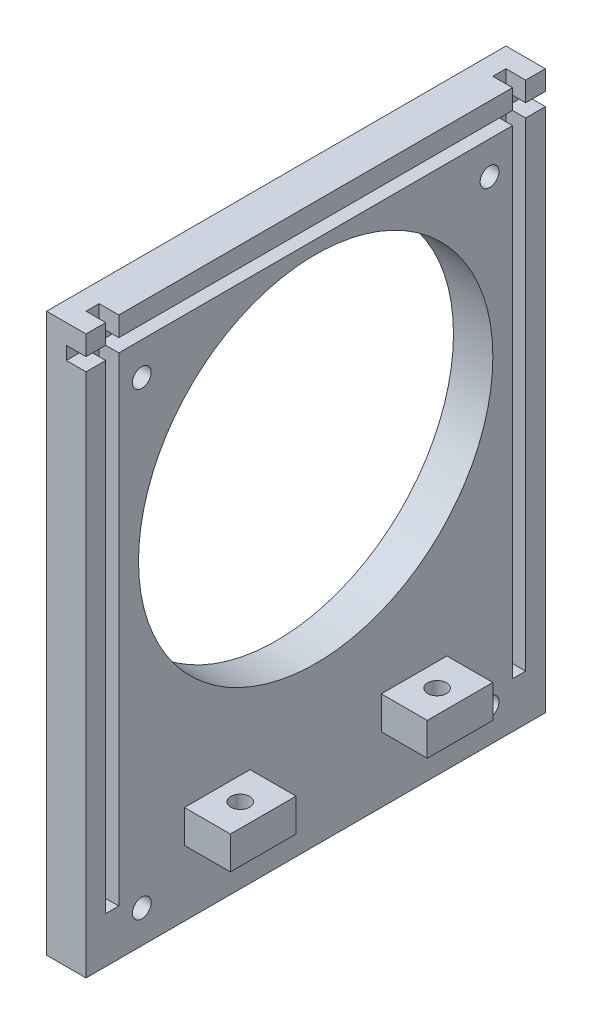
SolidWorks part; units mm, degrees
ref_plane "Alzado" through (0, 0, 0) normal (0, 0, 1) x (1, 0, 0)
ref_plane "Planta" through (0, 0, 0) normal (0, 1, 0) x (1, 0, 0)
ref_plane "Vista lateral" through (0, 0, 0) normal (1, 0, 0) x (0, 0, -1)
sketch "Croquis1" plane through (0, 0, 0) normal (0, 1, 0) x (1, 0, 0)
  line L1 (-3, 35) -> (3, 35)
  line L2 (-3, 35) -> (-3, -35)
  line L3 (-3, -35) -> (3, -35)
  line L4 (3, 35) -> (3, -35)
  line L5 (-3, 35) -> (3, -35) construction
  line L6 (-3, -35) -> (3, 35) construction
  point P0 (0, 0)
  dimension "D1" = 70
  dimension "D2" = 6
extrude "Saliente-Extruir1" add sketch "Croquis1" along normal blind 10
sketch "Croquis2" plane through (0, 10, 0) normal (0, 1, 0) x (1, 0, 0)
  line L0 (-3, -35) -> (3, -35) construction
  line L1 (-3, 35) -> (3, 35)
  line L2 (-3, 35) -> (-3, -35)
  line L3 (-3, -35) -> (3, -35)
  line L4 (3, 35) -> (3, -35)
  dimension "D1" = 6
extrude "Saliente-Extruir2" add sketch "Croquis2" along normal blind 75
sketch "Croquis3" plane through (3, 0, 0) normal (1, 0, 0) x (0, 0, -1)
  line L0 (-35, 85) -> (35, 85) construction
  line L1 (-32, 85) -> (-30, 85)
  line L2 (-32, 85) -> (-32, 7)
  line L3 (-32, 7) -> (-30, 7)
  line L4 (-30, 85) -> (-30, 7)
  line L6 (-35, 85) -> (-35, 0) construction
  dimension "D1" = 3
  dimension "D2" = 2
  dimension "D3" = 78
extrude "Cortar-Extruir1" cut sketch "Croquis3" against normal blind 3
mirror "Simetría1" about plane through (0, 0, 0) normal (0, 0, 1) of "Cortar-Extruir1"
sketch "Croquis4" plane through (3, 0, 0) normal (1, 0, 0) x (0, 0, -1)
  line L0 (-35, 85) -> (-35, 0) construction
  line L1 (-35, 82) -> (35, 82)
  line L2 (-35, 82) -> (-35, 80)
  line L3 (-35, 80) -> (35, 80)
  line L4 (35, 82) -> (35, 80)
  line L5 (35, 85) -> (35, 0) construction
  line L6 (-30, 85) -> (30, 85) construction
  dimension "D1" = 3
  dimension "D2" = 2
extrude "Cortar-Extruir2" cut sketch "Croquis4" against normal blind 3
sketch "Croquis5" plane through (3, 0, 0) normal (1, 0, 0) x (0, 0, -1)
  line L1 (30, 7) -> (30, 80) construction
  line L2 (-30, 85) -> (30, 85) construction
  circle A0 centre (0, 51) radius 27
  dimension "D1" = 54
  dimension "D2" = 34
  dimension "D3" = 30
extrude "Cortar-Extruir3" cut sketch "Croquis5" against normal up to next
sketch "Croquis8" plane through (-3, 0, 0) normal (-1, 0, 0) x (0, 0, 1)
  line L0 (35, 85) -> (35, 0) construction
  line L1 (-35, 85) -> (35, 85) construction
  circle A0 centre (26.5, 75) radius 1.435
  dimension "D3" = 2.87
  dimension "D1" = 8.5
  dimension "D2" = 10
extrude "Cortar-Extruir5" cut sketch "Croquis8" against normal blind 15
pattern_linear "MatrizL1" count 2 spacing 70 along (0, -1, 0) count 2 spacing 53 along (0, 0, -1) of "Cortar-Extruir5"
sketch "Croquis12" plane through (3, 0, 0) normal (1, 0, 0) x (0, 0, -1)
  line L1 (-20, 15) -> (-10, 15)
  line L2 (-20, 15) -> (-20, 10)
  line L3 (-20, 10) -> (-10, 10)
  line L4 (-10, 15) -> (-10, 10)
  line L5 (-35, 80) -> (-35, 0) construction
  line L8 (-35, 0) -> (35, 0) construction
  dimension "D1" = 5
  dimension "D2" = 10
  dimension "D3" = 10
  dimension "D4" = 15
extrude "Saliente-Extruir3" add sketch "Croquis12" along normal blind 7
mirror "Simetría4" about plane through (0, 0, 0) normal (0, 0, 1) of "Saliente-Extruir3"
sketch "Croquis13" plane through (0, 15, 0) normal (0, 1, 0) x (1, 0, 0)
  line L0 (10, -10) -> (10, -20) construction
  line L1 (10, -10) -> (3, -10) construction
  circle A0 centre (6.5, -15) radius 1.435
  dimension "D1" = 2.87
  dimension "D2" = 3.5
  dimension "D3" = 5
extrude "Cortar-Extruir10" cut sketch "Croquis13" against normal up to next (5 mm away)
mirror "Simetría5" about plane through (0, 0, 0) normal (0, 0, 1) of "Cortar-Extruir10"
